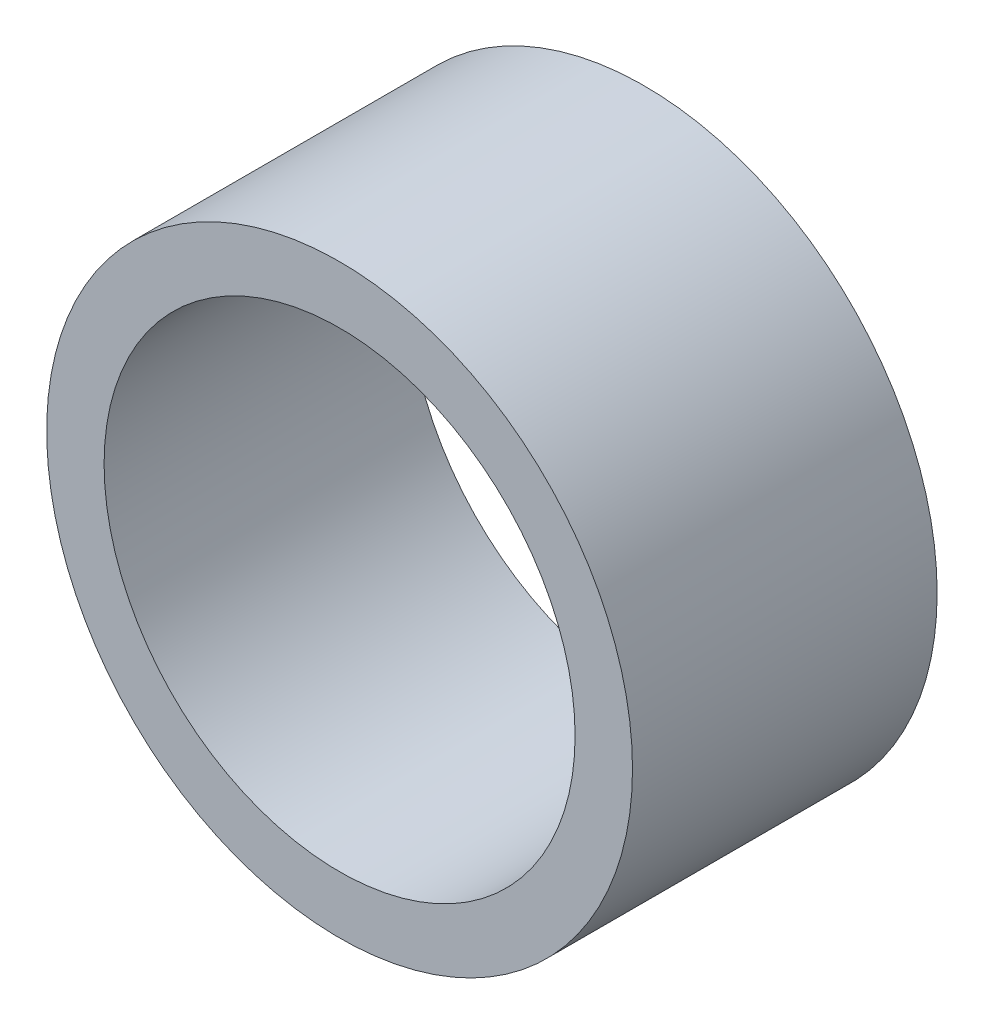
SolidWorks part; units mm, degrees
material "AISI 316 Stainless Steel Sheet (SS)"
ref_plane "Front Plane" through (0, 0, 0) normal (0, 0, 1) x (1, 0, 0)
ref_plane "Top Plane" through (0, 0, 0) normal (0, 1, 0) x (1, 0, 0)
ref_plane "Right Plane" through (0, 0, 0) normal (1, 0, 0) x (0, 0, -1)
sketch "Sketch1" plane through (0, 0, 0) normal (0, 0, 1) x (1, 0, 0)
  line L0 (6.35, 0) -> (-6.35, 0) construction
  line L1 (0, -5.1054) -> (0, 5.1054) construction
  line L2 (0, -6.35) -> (0, 6.35) construction
  circle A0 centre (0, 0) radius 6.35 construction
  circle A1 centre (0, 0) radius 5.1054 construction
  point P6 (0, 0)
  point P7 (-5.1054, 0)
  point P8 (5.1054, 0)
  point P10 (-6.35, 0)
  point P11 (6.35, 0)
  point P14 (0, 0)
  point P17 (0, 0)
  point P18 (0, 5.1054)
  point P19 (0, 6.35)
  point P20 (0, -5.1054)
  point P21 (0, -6.35)
  dimension "OD" = 12.7
  dimension "ID" = 10.2108
  dimension "Wall Thickness" = 1.2446
sketch "Sketch2" plane through (0, 0, 0) normal (1, 0, 0) x (0, 0, -1)
  line L0 (0, -5.1054) -> (0, 5.1054) construction
  line L1 (0, -5.1054) -> (0, 5.1054) construction
  line L2 (0, -6.35) -> (0, 6.35) construction
  line L3 (0, -6.35) -> (0, 6.35) construction
  line L4 (3.302, 6.35) -> (-3.302, 6.35) construction
  line L5 (3.302, 5.1054) -> (-3.302, 5.1054) construction
  line L6 (3.302, -5.1054) -> (-3.302, -5.1054) construction
  line L7 (3.302, -6.35) -> (-3.302, -6.35) construction
  line L8 (-3.302, -6.35) -> (-3.302, 6.35) construction
  line L9 (3.302, 6.35) -> (3.302, -6.35) construction
  line L10 (3.302, 0) -> (-3.302, 0) construction
  line L11 (2.3424, -6.35) -> (2.3424, 6.35) construction
  line L12 (-2.3424, -6.35) -> (-2.3424, 6.35) construction
  point P7 (0, 6.35)
  point P10 (0, 5.1054)
  point P13 (0, -5.1054)
  point P16 (0, -6.35)
  point P17 (-3.302, -6.35)
  point P18 (-3.302, -5.1054)
  point P19 (-3.302, 5.1054)
  point P20 (-3.302, 6.35)
  point P21 (3.302, 6.35)
  point P22 (3.302, 5.1054)
  point P23 (3.302, -5.1054)
  point P24 (3.302, -6.35)
  point P28 (0, 0)
  point P30 (2.3424, 0)
  point P31 (2.3424, -6.35)
  point P32 (2.3424, 6.35)
  point P35 (-2.3424, 0)
  point P36 (-2.3424, 6.35)
  point P37 (-2.3424, -6.35)
  dimension "Length" = 6.604
  dimension "Break Line" = 5.6444
sketch "Sketch3" plane through (0, 0, 0) normal (0, 0, 1) x (1, 0, 0)
  circle A0 centre (0, 0) radius 5.1054 construction
  circle A1 centre (0, 0) radius 6.35 construction
  circle A2 centre (0, 0) radius 5.1054
  circle A3 centre (0, 0) radius 6.35
extrude "Boss-Extrude1" add sketch "Sketch3" along normal up to vertex (3.302 mm away) and the other way up to vertex (3.302 mm away) up to point (0, 0, 3.302) other way up to point (0, 0, -3.302)
equation "\"Break Line@Sketch2\"=\"OD@Sketch1\"/2.25"
